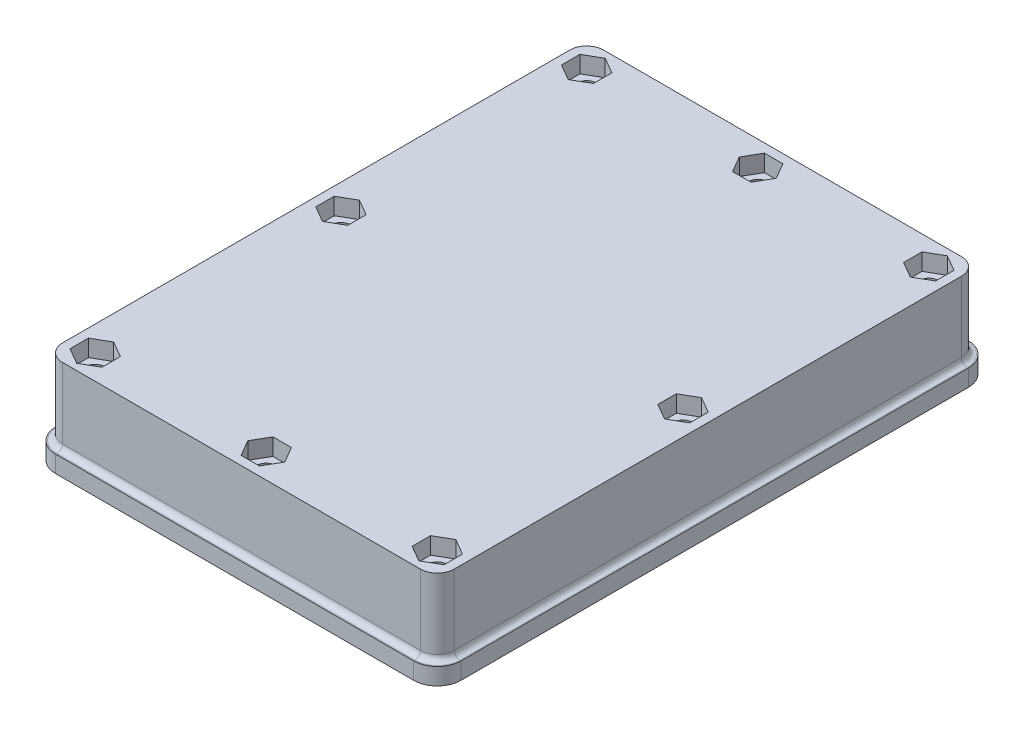
SolidWorks part; units mm, degrees
ref_plane "Спереди" through (0, 0, 0) normal (0, 0, 1) x (1, 0, 0)
ref_plane "Сверху" through (0, 0, 0) normal (0, 1, 0) x (1, 0, 0)
ref_plane "Справа" through (0, 0, 0) normal (1, 0, 0) x (0, 0, -1)
sketch "Эскиз1" plane through (0, 0, 0) normal (0, 1, 0) x (1, 0, 0)
  line L0 (-22.9993, -47.5511) -> (40.5007, -47.5511)
  line L1 (43.5007, 45.4489) -> (43.5007, -44.5511)
  line L2 (-25.9993, 45.4489) -> (-25.9993, -44.5511)
  line L3 (-22.9993, 48.4489) -> (40.5007, 48.4489)
  line L6 (-15.9993, 40.4489) -> (38.0007, 40.4489)
  line L7 (38.0007, 10.4489) -> (38.0007, 40.4489)
  line L8 (35.5007, 10.4489) -> (38.0007, 10.4489)
  line L9 (35.5007, 10.4489) -> (35.5007, -29.0511)
  line L10 (35.5007, -39.5511) -> (35.5007, -30.0511)
  line L11 (27.5007, -39.5511) -> (35.5007, -39.5511)
  line L12 (27.5007, -30.0511) -> (27.5007, -39.5511)
  line L13 (21.0007, -30.0511) -> (27.5007, -30.0511)
  line L15 (-15.9993, -31.5511) -> (21.0007, -31.5511)
  line L20 (-15.9993, -31.5511) -> (-15.9993, 40.4489)
  line L25 (21.0007, -31.5511) -> (21.0007, -30.0511)
  line L26 (35.5007, -29.0511) -> (35.5007, -30.0511)
  circle A0 centre (-21.5993, 0.4489) radius 1.7
  arc A1 (-22.9993, 48.4489) -> (-25.9993, 45.4489) centre (-22.9993, 45.4489) ccw
  circle A2 centre (-21.5993, -43.1511) radius 1.7
  circle A3 centre (8.7507, -43.1511) radius 1.7
  arc A4 (40.5007, -47.5511) -> (43.5007, -44.5511) centre (40.5007, -44.5511) ccw
  circle A5 centre (39.1007, -43.1511) radius 1.7
  circle A6 centre (39.1007, 0.4489) radius 1.7
  arc A7 (43.5007, 45.4489) -> (40.5007, 48.4489) centre (40.5007, 45.4489) ccw
  circle A8 centre (39.1007, 44.0489) radius 1.7
  circle A9 centre (8.7507, 44.0489) radius 1.7
  circle A10 centre (-21.5993, 44.0489) radius 1.7
  arc A11 (-22.9993, -47.5511) -> (-25.9993, -44.5511) centre (-22.9993, -44.5511) cw
  point P13 (43.5007, 0.4489)
  point P35 (-15.9993, 4.4489)
  dimension "D3" = 10
  dimension "D6" = 60.7
  dimension "D7" = 3
  dimension "D1" = 51.5
  dimension "D2" = 8
  dimension "D4" = 60.7
  dimension "D5" = 60.7
  dimension "D9" = 30.35
  dimension "D10" = 30.35
extrude "Бобышка-Вытянуть1" add sketch "Эскиз1" along normal blind 12.5
sketch "Эскиз2" plane through (0, 12.5, 0) normal (0, 1, 0) x (1, 0, 0)
  line L4 (-22.9993, -47.5511) -> (40.5007, -47.5511) construction
  line L5 (-25.9993, 45.4489) -> (-25.9993, -44.5511) construction
  line L6 (43.5007, 45.4489) -> (43.5007, -44.5511) construction
  line L7 (-22.9993, 48.4489) -> (40.5007, 48.4489) construction
  line L8 (-22.9993, -47.5511) -> (40.5007, -47.5511)
  line L9 (-25.9993, 45.4489) -> (-25.9993, -44.5511)
  line L10 (43.5007, 45.4489) -> (43.5007, -44.5511)
  line L11 (-22.9993, 48.4489) -> (40.5007, 48.4489)
  circle A4 centre (39.1007, -43.1511) radius 1.7 construction
  arc A5 (40.5007, -47.5511) -> (43.5007, -44.5511) centre (40.5007, -44.5511) ccw construction
  circle A6 centre (8.7507, -43.1511) radius 1.7 construction
  circle A7 centre (-21.5993, -43.1511) radius 1.7 construction
  arc A16 (-25.9993, -44.5511) -> (-22.9993, -47.5511) centre (-22.9993, -44.5511) ccw construction
  circle A17 centre (-21.5993, 0.4489) radius 1.7 construction
  circle A18 centre (39.1007, 0.4489) radius 1.7 construction
  arc A19 (-22.9993, 48.4489) -> (-25.9993, 45.4489) centre (-22.9993, 45.4489) ccw construction
  circle A20 centre (-21.5993, 44.0489) radius 1.7 construction
  circle A21 centre (8.7507, 44.0489) radius 1.7 construction
  circle A22 centre (39.1007, 44.0489) radius 1.7 construction
  arc A23 (43.5007, 45.4489) -> (40.5007, 48.4489) centre (40.5007, 45.4489) ccw construction
  circle A24 centre (39.1007, -43.1511) radius 1.7
  arc A25 (40.5007, -47.5511) -> (43.5007, -44.5511) centre (40.5007, -44.5511) ccw
  circle A26 centre (8.7507, -43.1511) radius 1.7
  circle A27 centre (-21.5993, -43.1511) radius 1.7
  arc A28 (-25.9993, -44.5511) -> (-22.9993, -47.5511) centre (-22.9993, -44.5511) ccw
  circle A29 centre (-21.5993, 0.4489) radius 1.7
  circle A30 centre (39.1007, 0.4489) radius 1.7
  arc A31 (-22.9993, 48.4489) -> (-25.9993, 45.4489) centre (-22.9993, 45.4489) ccw
  circle A32 centre (-21.5993, 44.0489) radius 1.7
  circle A33 centre (8.7507, 44.0489) radius 1.7
  circle A34 centre (39.1007, 44.0489) radius 1.7
  arc A35 (43.5007, 45.4489) -> (40.5007, 48.4489) centre (40.5007, 45.4489) ccw
extrude "Бобышка-Вытянуть2" add sketch "Эскиз2" along normal blind 2
sketch "Эскиз8" plane through (0, 10, 0) normal (0, -1, 0) x (1, 0, 0)
  line L0 (35.5007, -5.2489) -> (35.5007, 4.3511)
  line L1 (35.5007, -10.4489) -> (35.5007, 39.5511) construction
  line L2 (35.5007, -40.4489) -> (35.5007, 30.0511) construction
  arc A1 (35.5007, 4.3511) -> (35.5007, -5.2489) centre (39.1007, -0.4489) ccw
  dimension "D2" = 12
extrude "Бобышка-Вытянуть5" add sketch "Эскиз8" along normal blind 2 from surface at -2.5 starting at face at (21.2007, 12.5, 10.0511)
sketch "Эскиз9" plane through (0, 0, 0) normal (0, -1, 0) x (1, 0, 0)
  line L4 (-22.9993, 47.5511) -> (40.5007, 47.5511) construction
  line L5 (-25.9993, -45.4489) -> (-25.9993, 44.5511) construction
  line L6 (-22.9993, -48.4489) -> (40.5007, -48.4489) construction
  line L7 (43.5007, -45.4489) -> (43.5007, 44.5511) construction
  line L8 (43.5007, -45.4489) -> (43.5007, 44.5511)
  line L9 (-22.9993, -48.4489) -> (40.5007, -48.4489)
  line L10 (-25.9993, -45.4489) -> (-25.9993, 44.5511)
  line L11 (-22.9993, 47.5511) -> (40.5007, 47.5511)
  arc A4 (-25.9993, -45.4489) -> (-22.9993, -48.4489) centre (-22.9993, -45.4489) ccw construction
  arc A5 (-22.9993, 47.5511) -> (-25.9993, 44.5511) centre (-22.9993, 44.5511) ccw construction
  arc A14 (43.5007, 44.5511) -> (40.5007, 47.5511) centre (40.5007, 44.5511) ccw construction
  arc A15 (40.5007, -48.4489) -> (43.5007, -45.4489) centre (40.5007, -45.4489) ccw construction
  arc A24 (43.5007, 44.5511) -> (40.5007, 47.5511) centre (40.5007, 44.5511) ccw
  arc A25 (40.5007, -48.4489) -> (43.5007, -45.4489) centre (40.5007, -45.4489) ccw
  arc A26 (-25.9993, -45.4489) -> (-22.9993, -48.4489) centre (-22.9993, -45.4489) ccw
  arc A27 (-22.9993, 47.5511) -> (-25.9993, 44.5511) centre (-22.9993, 44.5511) ccw
extrude "Вытянуть-Тонкостенный1" add sketch "Эскиз9" along normal blind 2 thin thin type one direction reverse wall 1.3
sketch "Эскиз11" plane through (0, -2, 0) normal (0, -1, 0) x (1, 0, 0)
  line L4 (-22.9993, -47.1489) -> (40.5007, -47.1489) construction
  line L5 (-24.6993, 44.5511) -> (-24.6993, -45.4489) construction
  line L6 (42.2007, -45.4489) -> (42.2007, 44.5511) construction
  line L7 (40.5007, 46.2511) -> (-22.9993, 46.2511) construction
  line L8 (-22.9993, -47.1489) -> (40.5007, -47.1489)
  line L9 (-24.6993, 44.5511) -> (-24.6993, -45.4489)
  line L10 (42.2007, -45.4489) -> (42.2007, 44.5511)
  line L11 (40.5007, 46.2511) -> (-22.9993, 46.2511)
  arc A4 (40.5007, -47.1489) -> (42.2007, -45.4489) centre (40.5007, -45.4489) ccw construction
  arc A5 (-24.6993, -45.4489) -> (-22.9993, -47.1489) centre (-22.9993, -45.4489) ccw construction
  arc A6 (-22.9993, 46.2511) -> (-24.6993, 44.5511) centre (-22.9993, 44.5511) ccw construction
  arc A7 (42.2007, 44.5511) -> (40.5007, 46.2511) centre (40.5007, 44.5511) ccw construction
  arc A8 (40.5007, -47.1489) -> (42.2007, -45.4489) centre (40.5007, -45.4489) ccw
  arc A9 (-24.6993, -45.4489) -> (-22.9993, -47.1489) centre (-22.9993, -45.4489) ccw
  arc A10 (-22.9993, 46.2511) -> (-24.6993, 44.5511) centre (-22.9993, 44.5511) ccw
  arc A11 (42.2007, 44.5511) -> (40.5007, 46.2511) centre (40.5007, 44.5511) ccw
extrude "Вытянуть-Тонкостенный3" add sketch "Эскиз11" against normal blind 3 thin
fillet "Скругление4" radius 1 8 edges at (42.6221, 1, 46.6725) (8.7507, 1, 47.5511) (-25.9993, 1, -0.4489) (8.7507, 1, -48.4489) (42.6221, 1, -47.5702) (43.5007, 1, -0.4489) (-25.1206, 1, 46.6725) (-25.1206, 1, -47.5702)
sketch "Эскиз12" plane through (0, 0, 0) normal (0, -1, 0) x (1, 0, 0)
  line L0 (-15.9993, 31.5511) -> (19.9428, 28.8598)
  line L1 (19.9428, 28.8598) -> (27.5007, 28.8598)
  line L2 (27.5007, 28.8598) -> (27.5007, 38.4511)
  line L3 (-15.9993, 31.5511) -> (-15.9993, 38.4511)
  line L4 (-15.9993, 38.4511) -> (27.5007, 38.4511)
  circle A0 centre (8.7507, 43.1511) radius 1.7 construction
  point P0 (8.7507, 41.4511)
  point P1 (8.7507, 38.4511)
  dimension "D1" = 3
extrude "Вырез-Вытянуть1" cut sketch "Эскиз12" against normal up to surface (12.5 mm away) up to face at (23.3841, 12.5, 8.3011)
sketch "Эскиз13" plane through (0, 0, 0) normal (0, -1, 0) x (1, 0, 0)
  line L0 (8.7507, -49.6489) -> (8.7507, 48.7511) construction
  line L1 (-22.9993, -49.6489) -> (40.5007, -49.6489) construction
  line L2 (40.5007, 48.7511) -> (-22.9993, 48.7511) construction
  line L3 (-18.4493, -5.9489) -> (35.9507, -5.9489)
  line L4 (-18.4493, -5.9489) -> (-18.4493, -40.4489)
  line L5 (-18.4493, -40.4489) -> (35.9507, -40.4489)
  line L6 (35.9507, -5.9489) -> (35.9507, -40.4489)
  line L7 (-18.4493, -5.9489) -> (35.9507, -40.4489) construction
  line L8 (-18.4493, -40.4489) -> (35.9507, -5.9489) construction
  line L9 (-15.9993, -40.4489) -> (38.0007, -40.4489) construction
  point P2 (8.7507, -40.4489)
  point P3 (8.7507, -23.1989)
  point P13 (8.7507, -40.4489)
  dimension "D3" = 34.5
  dimension "D4" = 54.4
extrude "Вырез-Вытянуть2" cut sketch "Эскиз13" against normal up to surface (12.5 mm away) up to face at (23.8607, 12.5, 5.3311)
sketch "Эскиз14" plane through (0, 0, 0) normal (0, -1, 0) x (1, 0, 0)
  line L0 (35.9507, -40.4489) -> (38.0007, -40.4489)
  line L1 (38.0007, -40.4489) -> (38.0007, -5.9489)
  line L2 (38.0007, -5.9489) -> (35.5007, -5.9489)
  line L3 (35.5007, -5.9489) -> (35.9507, -40.4489)
extrude "Вырез-Вытянуть3" cut sketch "Эскиз14" against normal up to surface (12.5 mm away) up to face at (19.5436, 12.5, 2.1083)
sketch "Эскиз15" plane through (-18.4493, 0, 0) normal (1, 0, 0) x (0, 0, -1)
  line L0 (5.9489, 12.5) -> (40.4489, 12.5) construction
  line L1 (37.3989, 5.9) -> (8.9989, 5.9)
  line L2 (23.1989, 12.5) -> (23.1989, 0) construction
  line L3 (5.9489, 0) -> (40.4489, 0) construction
  line L4 (40.4489, 12.5) -> (40.4489, 0) construction
  line L6 (40.4489, 4) -> (5.9489, 4)
  line L7 (40.4489, 4) -> (40.4489, 8.5151)
  line L8 (5.9489, 12.5) -> (5.9489, 0) construction
  line L9 (5.9489, 4) -> (5.9489, 8.5151)
  line L10 (5.9489, 12.5) -> (40.4489, 12.5)
  line L11 (37.3989, 12) -> (8.9989, 12)
  line L12 (40.4489, 8.5151) -> (40.4177, 8.5151)
  line L13 (5.98, 8.5151) -> (5.9489, 8.5151)
  line L14 (40.4489, 9.4446) -> (40.4085, 9.4446)
  line L15 (5.9892, 9.4446) -> (5.9489, 9.4446)
  line L16 (40.4489, 9.4446) -> (40.4489, 12.5)
  line L17 (5.9489, 9.4446) -> (5.9489, 12.5)
  arc A0 (37.3989, 5.9) -> (40.4177, 8.5151) centre (37.3989, 8.95) ccw
  arc A1 (8.9989, 12) -> (5.9892, 9.4446) centre (8.9989, 8.95) ccw
  arc A2 (5.98, 8.5151) -> (8.9989, 5.9) centre (8.9989, 8.95) ccw
  arc A3 (40.4085, 9.4446) -> (37.3989, 12) centre (37.3989, 8.95) ccw
  point P3 (37.3989, 12)
  point P4 (40.4489, 8.95)
  point P8 (5.9489, 8.95)
  dimension "D1" = 6.1
  dimension "D2" = 0.5
sketch "Эскиз19" plane through (0, 14.5, 0) normal (0, 1, 0) x (1, 0, 0)
  line L0 (8.7507, 48.4489) -> (8.7507, -47.5511) construction
  line L1 (40.5007, 48.4489) -> (-22.9993, 48.4489) construction
  line L2 (-22.9993, -47.5511) -> (40.5007, -47.5511) construction
  line L3 (-25.9993, 0.4489) -> (43.5007, 0.4489) construction
  line L4 (-25.9993, 45.4489) -> (-25.9993, -44.5511) construction
  line L5 (43.5007, -44.5511) -> (43.5007, 45.4489) construction
  line L7 (-21.5993, 40.7753) -> (-18.7643, 42.4121)
  line L8 (-18.7643, 42.4121) -> (-18.7643, 45.6857)
  line L9 (-18.7643, 45.6857) -> (-21.5993, 47.3224)
  line L10 (-21.5993, 47.3224) -> (-24.4343, 45.6857)
  line L11 (-24.4343, 45.6857) -> (-24.4343, 42.4121)
  line L12 (-24.4343, 42.4121) -> (-21.5993, 40.7753)
  line L13 (-21.5993, -2.8247) -> (-18.7643, -1.1879)
  line L14 (-18.7643, -1.1879) -> (-18.7643, 2.0857)
  line L15 (-18.7643, 2.0857) -> (-21.5993, 3.7224)
  line L16 (-21.5993, 3.7224) -> (-24.4343, 2.0857)
  line L17 (-24.4343, 2.0857) -> (-24.4343, -1.1879)
  line L18 (-24.4343, -1.1879) -> (-21.5993, -2.8247)
  line L19 (5.4772, 44.0489) -> (7.1139, 41.2139)
  line L20 (7.1139, 41.2139) -> (10.3875, 41.2139)
  line L21 (10.3875, 41.2139) -> (12.0243, 44.0489)
  line L22 (12.0243, 44.0489) -> (10.3875, 46.8839)
  line L23 (10.3875, 46.8839) -> (7.1139, 46.8839)
  line L24 (7.1139, 46.8839) -> (5.4772, 44.0489)
  line L25 (39.1007, 40.7753) -> (41.9357, 42.4121)
  line L26 (41.9357, 42.4121) -> (41.9357, 45.6857)
  line L27 (41.9357, 45.6857) -> (39.1007, 47.3224)
  line L28 (39.1007, 47.3224) -> (36.2657, 45.6857)
  line L29 (36.2657, 45.6857) -> (36.2657, 42.4121)
  line L30 (36.2657, 42.4121) -> (39.1007, 40.7753)
  line L31 (39.1007, -2.8247) -> (41.9357, -1.1879)
  line L32 (41.9357, -1.1879) -> (41.9357, 2.0857)
  line L33 (41.9357, 2.0857) -> (39.1007, 3.7224)
  line L34 (39.1007, 3.7224) -> (36.2657, 2.0857)
  line L35 (36.2657, 2.0857) -> (36.2657, -1.1879)
  line L36 (36.2657, -1.1879) -> (39.1007, -2.8247)
  line L37 (-21.5993, -39.8776) -> (-24.4343, -41.5143)
  line L38 (-24.4343, -41.5143) -> (-24.4343, -44.7879)
  line L39 (-24.4343, -44.7879) -> (-21.5993, -46.4247)
  line L40 (-21.5993, -46.4247) -> (-18.7643, -44.7879)
  line L41 (-18.7643, -44.7879) -> (-18.7643, -41.5143)
  line L42 (-18.7643, -41.5143) -> (-21.5993, -39.8776)
  line L43 (5.4772, -43.1511) -> (7.1139, -45.9861)
  line L44 (7.1139, -45.9861) -> (10.3875, -45.9861)
  line L45 (10.3875, -45.9861) -> (12.0243, -43.1511)
  line L46 (12.0243, -43.1511) -> (10.3875, -40.3161)
  line L47 (10.3875, -40.3161) -> (7.1139, -40.3161)
  line L48 (7.1139, -40.3161) -> (5.4772, -43.1511)
  line L49 (39.1007, -39.8776) -> (36.2657, -41.5143)
  line L50 (36.2657, -41.5143) -> (36.2657, -44.7879)
  line L51 (36.2657, -44.7879) -> (39.1007, -46.4247)
  line L52 (39.1007, -46.4247) -> (41.9357, -44.7879)
  line L53 (41.9357, -44.7879) -> (41.9357, -41.5143)
  line L54 (41.9357, -41.5143) -> (39.1007, -39.8776)
  circle A0 centre (-21.5993, 44.0489) radius 2.835 construction
  circle A1 centre (-21.5993, 0.4489) radius 2.835 construction
  circle A2 centre (8.7507, 44.0489) radius 2.835 construction
  circle A3 centre (39.1007, 44.0489) radius 2.835 construction
  circle A4 centre (39.1007, 0.4489) radius 2.835 construction
  circle A5 centre (-21.5993, -43.1511) radius 2.835 construction
  circle A6 centre (8.7507, -43.1511) radius 2.835 construction
  circle A7 centre (39.1007, -43.1511) radius 2.835 construction
  point P76 (-24.4343, 44.0489)
  point P85 (-18.7643, 44.0489)
  point P86 (-24.4343, -43.1511)
  point P87 (-18.7643, -43.1511)
  point P88 (36.2657, 44.0489)
  point P89 (41.9357, 44.0489)
  point P90 (36.2657, 0.4489)
  point P91 (36.2657, -43.1511)
  point P92 (41.9357, -43.1511)
  dimension "D1" = 5.67
  dimension "D2" = 5.67
  dimension "D3" = 5.67
  dimension "D4" = 5.67
  dimension "D5" = 5.67
  dimension "D6" = 5.67
extrude "Вырез-Вытянуть5" cut sketch "Эскиз19" against normal blind 3
extrude "Бобышка-Вытянуть11" add sketch "Эскиз15" along normal blind 3
sketch "Эскиз22" plane through (0, 4, 0) normal (0, -1, 0) x (1, 0, 0)
  line L0 (-15.4493, -40.4489) -> (-18.4493, -40.4489) construction
  line L1 (-18.4493, -40.4489) -> (38.0007, -40.4489) construction
  line L2 (-18.4493, -5.9489) -> (-18.4493, -40.4489) construction
  line L3 (-18.4493, -5.9489) -> (-18.4493, -40.4489) construction
  circle A0 centre (-17.9493, -35.9489) radius 0.5
  circle A1 centre (-17.9493, -29.1489) radius 0.5
  dimension "D1" = 1
  dimension "D2" = 1
  dimension "D3" = 4.5
  dimension "D4" = 11.3
extrude "Вырез-Вытянуть7" cut sketch "Эскиз22" against normal blind 1
sketch "Эскиз23" plane through (0, 12.5, 0) normal (0, -1, 0) x (1, 0, 0)
  line L0 (38.0007, -5.9489) -> (31.5507, -5.9489)
  line L1 (31.5507, -5.9489) -> (31.5507, -40.4489)
  line L2 (37.3007, -40.4489) -> (-15.4493, -40.4489) construction
  line L3 (31.5507, -40.4489) -> (38.0007, -40.4489)
  line L4 (38.0007, -40.4489) -> (38.0007, -5.9489)
  dimension "D1" = 50
extrude "Бобышка-Вытянуть12" add sketch "Эскиз23" along normal blind 0.5
sketch "Эскиз25" plane through (0, 12.5, 0) normal (0, -1, 0) x (1, 0, 0)
  line L0 (4.4817, -4.3632) -> (6.7909, -4.3632)
  line L1 (6.7909, -4.3632) -> (4.4817, -4.3632) construction
  line L2 (11.4106, -4.3632) -> (13.7198, -4.3632)
  arc A0 (11.4106, -4.3632) -> (6.7909, -4.3632) centre (9.1007, -2.4489) ccw
  arc A1 (13.7198, -4.3632) -> (4.4817, -4.3632) centre (9.1007, -2.4489) ccw
extrude "Бобышка-Вытянуть13" add sketch "Эскиз25" along normal blind 3 contours A0 L0 A1 L2
chamfer "Фаска2" distance 2 angle 15 2 edges at (12.5652, 9.5, -4.3632) (5.6363, 9.5, -4.3632)
fillet "Скругление7" radius 3 1 edges at (8.0507, 12.5, -40.4489)
